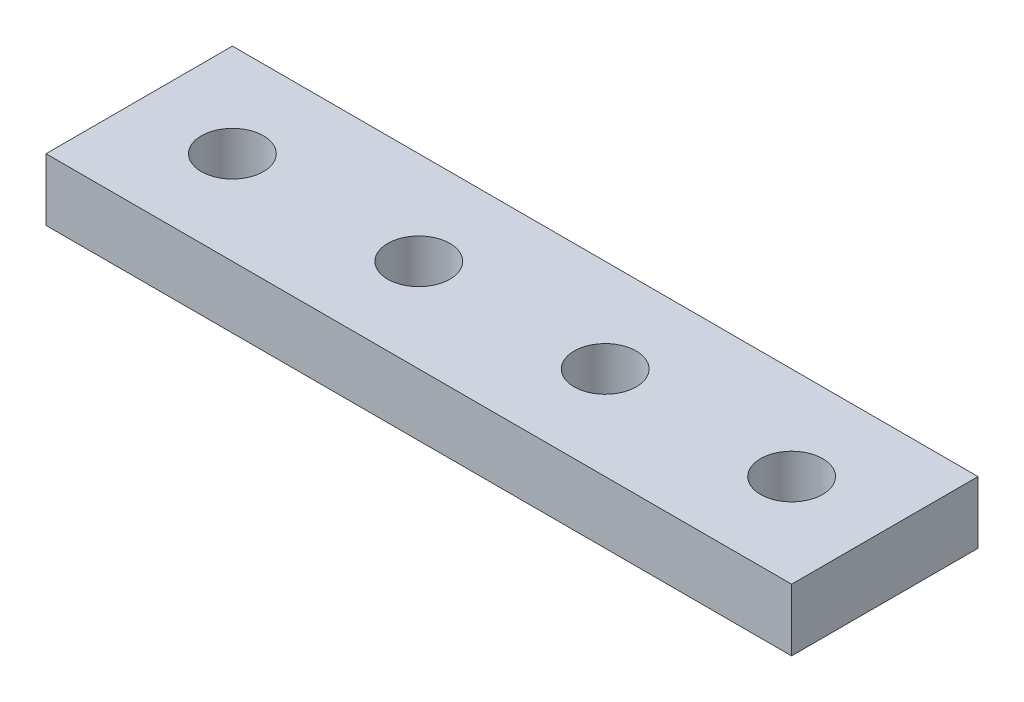
SolidWorks part; units mm, degrees
ref_plane "Front Plane" through (0, 0, 0) normal (0, 0, 1) x (1, 0, 0)
ref_plane "Top Plane" through (0, 0, 0) normal (0, 1, 0) x (1, 0, 0)
ref_plane "Right Plane" through (0, 0, 0) normal (1, 0, 0) x (0, 0, -1)
sketch "Sketch1" plane through (0, 0, 0) normal (0, 1, 0) x (1, 0, 0)
  line L1 (0, 0) -> (120, 0)
  line L2 (0, 0) -> (0, 30)
  line L3 (0, 30) -> (120, 30)
  line L4 (120, 0) -> (120, 30)
  dimension "D1" = 120
  dimension "D2" = 30
extrude "Boss-Extrude1" add sketch "Sketch1" along normal blind 10
sketch "Sketch2" plane through (0, 10, 0) normal (0, 1, 0) x (1, 0, 0)
  line L0 (0, 0) -> (120, 0) construction
  line L1 (0, 30) -> (0, 0) construction
  circle A0 centre (15, 15) radius 5
  dimension "D1" = 15
  dimension "D2" = 15
  dimension "D3" = 10
extrude "Cut-Extrude1" cut sketch "Sketch2" against normal through all
pattern_linear "LPattern1" count 4 spacing 30 along (1, 0, 0) count 4 spacing 30 along (0, 0, 1) of "Cut-Extrude1"
